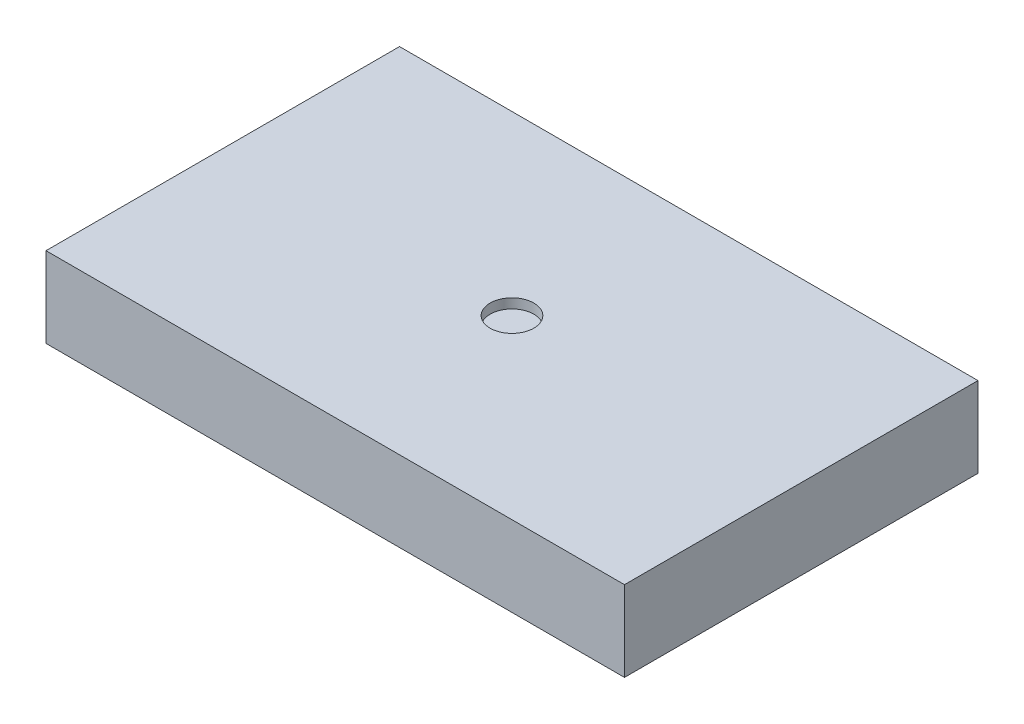
SolidWorks part; units mm, degrees
ref_plane "Front Plane" through (0, 0, 0) normal (0, 0, 1) x (1, 0, 0)
ref_plane "Top Plane" through (0, 0, 0) normal (0, 1, 0) x (1, 0, 0)
ref_plane "Right Plane" through (0, 0, 0) normal (1, 0, 0) x (0, 0, -1)
sketch "Sketch1" plane through (0, 0, 0) normal (0, 1, 0) x (1, 0, 0)
  line L1 (-22.86, -13.97) -> (22.86, -13.97)
  line L2 (-22.86, -13.97) -> (-22.86, 13.97)
  line L3 (-22.86, 13.97) -> (22.86, 13.97)
  line L4 (22.86, -13.97) -> (22.86, 13.97)
  line L5 (-22.86, -13.97) -> (22.86, 13.97) construction
  line L6 (-22.86, 13.97) -> (22.86, -13.97) construction
  point P0 (0, 0)
  dimension "D1" = 27.94
  dimension "D2" = 45.72
extrude "Boss-Extrude1" add sketch "Sketch1" along normal blind 6.35
sketch "Sketch2" plane through (0, 6.35, 0) normal (0, 1, 0) x (1, 0, 0)
  circle A0 centre (0, 0) radius 1.7248
extrude "Cut-Extrude1" cut sketch "Sketch2" against normal blind 0.762
